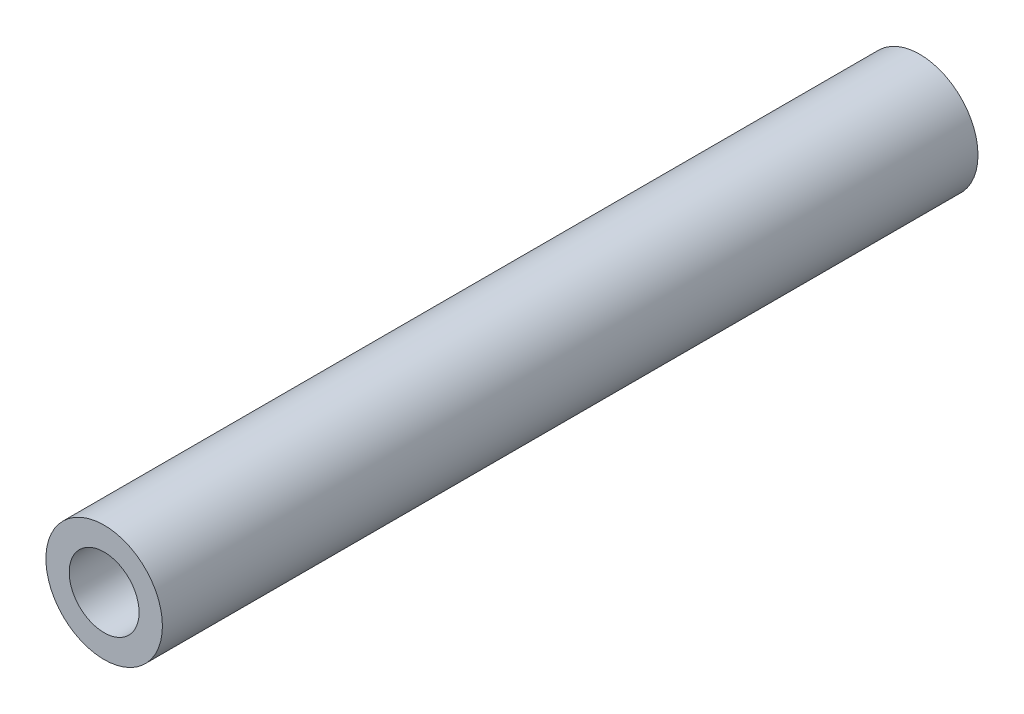
SolidWorks part; units mm, degrees
ref_plane "前视基准面" through (0, 0, 0) normal (0, 0, 1) x (1, 0, 0)
ref_plane "上视基准面" through (0, 0, 0) normal (0, 1, 0) x (1, 0, 0)
ref_plane "右视基准面" through (0, 0, 0) normal (1, 0, 0) x (0, 0, -1)
sketch "草图1" plane through (0, 0, 0) normal (0, 0, 1) x (1, 0, 0)
  circle A0 centre (0, 0) radius 2.5
  circle A1 centre (0, 0) radius 1.5
  dimension "D1" = 3
  dimension "D2" = 5
extrude "凸台-拉伸1" add sketch "草图1" along normal mid plane 35
